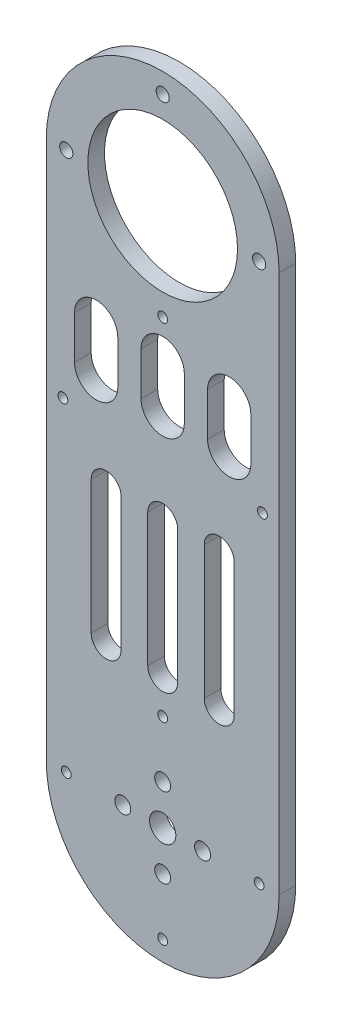
SolidWorks part; units mm, degrees
ref_plane "Front Plane" through (0, 0, 0) normal (0, 0, 1) x (1, 0, 0)
ref_plane "Top Plane" through (0, 0, 0) normal (0, 1, 0) x (1, 0, 0)
ref_plane "Right Plane" through (0, 0, 0) normal (1, 0, 0) x (0, 0, -1)
sketch "Sketch1" plane through (0, 0, 0) normal (0, 0, 1) x (1, 0, 0)
  line L0 (35, 0) -> (35, 162)
  line L1 (-35, 0) -> (-35, 162)
  line L2 (-35, 162) -> (35, 162) construction
  line L3 (0, 0) -> (35, 0) construction
  line L4 (0, 0) -> (0, 40) construction
  line L5 (0, 0) -> (25.0676, 25.0676) construction
  line L6 (0, 0) -> (0, 162) construction
  line L7 (0, 80) -> (0, 40) construction
  line L8 (4.5, 80) -> (4.5, 40)
  line L9 (-4.5, 80) -> (-4.5, 40)
  line L10 (0, 162) -> (0, 191) construction
  line L13 (17, 80) -> (17, 40) construction
  line L14 (21.5, 80) -> (21.5, 40)
  line L15 (12.5, 80) -> (12.5, 40)
  line L16 (-17, 80) -> (-17, 40) construction
  line L17 (-21.5, 80) -> (-21.5, 40)
  line L18 (-12.5, 80) -> (-12.5, 40)
  line L19 (0, 121.5) -> (0, 108.5) construction
  line L20 (6.5, 121.5) -> (6.5, 108.5)
  line L21 (-6.5, 121.5) -> (-6.5, 108.5)
  line L22 (20, 120.9465) -> (20, 107.9465) construction
  line L23 (26.5, 120.9465) -> (26.5, 107.9465)
  line L24 (13.5, 120.9465) -> (13.5, 107.9465)
  line L25 (-20, 120.9465) -> (-20, 107.9465) construction
  line L26 (-26.5, 120.9465) -> (-26.5, 107.9465)
  line L27 (-13.5, 120.9465) -> (-13.5, 107.9465)
  line L28 (0, 162) -> (29, 162) construction
  line L29 (0, 162) -> (0, 133) construction
  line L30 (0, 162) -> (-29, 162) construction
  arc A0 (-35, 0) -> (35, 0) centre (0, 0) ccw
  arc A1 (35, 162) -> (-35, 162) centre (0, 162) ccw
  circle A2 centre (0, 0) radius 3.95
  arc A7 (4.5, 80) -> (-4.5, 80) centre (0, 80) ccw
  arc A8 (-4.5, 40) -> (4.5, 40) centre (0, 40) ccw
  circle A9 centre (0, 29) radius 1.475
  arc A12 (21.5, 80) -> (12.5, 80) centre (17, 80) ccw
  arc A13 (12.5, 40) -> (21.5, 40) centre (17, 40) ccw
  arc A14 (-21.5, 80) -> (-12.5, 80) centre (-17, 80) cw
  arc A15 (-12.5, 40) -> (-21.5, 40) centre (-17, 40) cw
  arc A16 (6.5, 121.5) -> (-6.5, 121.5) centre (0, 121.5) ccw
  arc A17 (-6.5, 108.5) -> (6.5, 108.5) centre (0, 108.5) ccw
  arc A18 (26.5, 120.9465) -> (13.5, 120.9465) centre (20, 120.9465) ccw
  arc A19 (13.5, 107.9465) -> (26.5, 107.9465) centre (20, 107.9465) ccw
  arc A20 (-26.5, 120.9465) -> (-13.5, 120.9465) centre (-20, 120.9465) cw
  arc A21 (-13.5, 107.9465) -> (-26.5, 107.9465) centre (-20, 107.9465) cw
  circle A22 centre (0, 162) radius 22.5
  circle A25 centre (0, 133) radius 1.475
  circle A26 centre (-30, 97) radius 1.475
  circle A27 centre (30, 97) radius 1.475
  circle A29 centre (29, 0) radius 1.475
  circle A30 centre (0, -29) radius 1.475
  circle A31 centre (-29, 0) radius 1.475
  circle A32 centre (0, 12) radius 2.4
  circle A33 centre (12, 0) radius 2.4
  circle A34 centre (0, -12) radius 2.4
  circle A35 centre (-12, 0) radius 2.4
  circle A36 centre (0, 191) radius 1.975
  circle A37 centre (29, 162) radius 1.975
  circle A39 centre (-29, 162) radius 1.975
  circle A40 centre (0, 133) radius 1.975 [skipped]
  point P13 (0, 60)
  point P21 (0, 0)
  point P36 (17, 60)
  point P41 (0, 115)
  point P44 (-17, 60)
  point P55 (20, 114.4465)
  point P65 (-20, 114.4465)
  point P71 (0, 162)
  point P87 (0, 0)
  point P92 (0, 0)
  dimension "D1" = 70
  dimension "D4" = 7.9
  dimension "D6" = 4
  dimension "D11" = 4.5
  dimension "D12" = 2.95
  dimension "D16" = 29
  dimension "D18" = 4.5
  dimension "D22" = 6.5
  dimension "D24" = 6.5
  dimension "D27" = 45
  dimension "D30" = 2.95
  dimension "D32" = 2.95
  dimension "D7" = 4.8
  dimension "D15" = 3.95
  dimension "D2" = 162
  dimension "D3" = 162
  dimension "D5" = 45
  dimension "D9" = 40
  dimension "D10" = 40
  dimension "D13" = 29
  dimension "D14" = 13.5
  dimension "D17" = 4
  dimension "D19" = 40
  dimension "D20" = 60
  dimension "D21" = 13
  dimension "D23" = 40.5
  dimension "D25" = 13
  dimension "D26" = 7
  dimension "D31" = 29
  dimension "D33" = 65
  dimension "D34" = 5
  dimension "D8" = 12
  dimension "D35" = 4
extrude "Boss-Extrude1" add sketch "Sketch1" along normal blind 5
